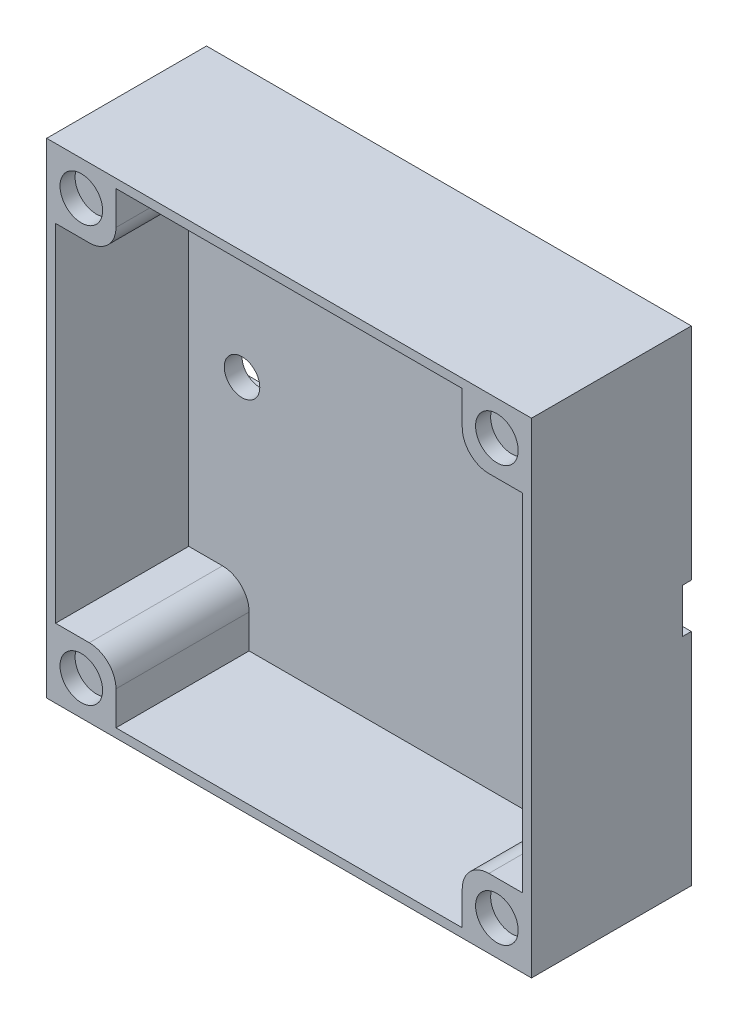
SolidWorks part; units mm, degrees
ref_plane "Přední rovina" through (0, 0, 0) normal (0, 0, 1) x (1, 0, 0)
ref_plane "Horní rovina" through (0, 0, 0) normal (0, 1, 0) x (1, 0, 0)
ref_plane "Pravá rovina" through (0, 0, 0) normal (1, 0, 0) x (0, 0, -1)
sketch "Skica1" plane through (0, 0, 0) normal (0, 0, 1) x (1, 0, 0)
  line L1 (27.3, 27.3) -> (-27.3, 27.3)
  line L2 (27.3, 27.3) -> (27.3, -27.3)
  line L3 (27.3, -27.3) -> (-27.3, -27.3)
  line L4 (-27.3, 27.3) -> (-27.3, -27.3)
  line L5 (27.3, 27.3) -> (-27.3, -27.3) construction
  line L6 (27.3, -27.3) -> (-27.3, 27.3) construction
  point P0 (0, 0)
  point P5 (-27.5, 0)
  point P11 (4.5, 0)
  dimension "D1" = 54.6
  dimension "D2" = 54.6
extrude "Přidat vysunutím2" add sketch "Skica1" along normal blind 3 contours L2 L1 L4 L3
sketch "Skica5" plane through (0, 0, 0) normal (0, 0, -1) x (-1, 0, 0)
  line L10 (27.3, 27.3) -> (27.3, -27.3) construction
  line L11 (-27.3, 2.5) -> (27.3, 2.5)
  line L12 (-27.3, 2.5) -> (-27.3, -2.5)
  line L13 (-27.3, -2.5) -> (27.3, -2.5)
  line L14 (27.3, 2.5) -> (27.3, -2.5)
  line L15 (-27.3, 2.5) -> (27.3, -2.5) construction
  line L16 (-27.3, -2.5) -> (27.3, 2.5) construction
  point P0 (0, 0)
  dimension "D1" = 5
extrude "Odebrat vysunutím3" cut sketch "Skica5" against normal blind 1 contours L11 L14 L13 L12
sketch "Skica14" plane through (0, 0, 3) normal (0, 0, 1) x (1, 0, 0)
  line L1 (-27.3, 27.3) -> (27.3, 27.3)
  line L2 (-27.3, 27.3) -> (-27.3, -27.3)
  line L3 (-27.3, -27.3) -> (27.3, -27.3)
  line L4 (27.3, 27.3) -> (27.3, -27.3)
  line L5 (-26.3, 26.3) -> (26.3, 26.3)
  line L6 (-26.3, 26.3) -> (-26.3, -27.3)
  line L7 (-26.3, -27.3) -> (26.3, -27.3)
  line L8 (26.3, 26.3) -> (26.3, -27.3)
  line L9 (-26.3, -27.3) -> (26.3, -27.3)
  line L10 (-26.3, -27.3) -> (-26.3, -26.3)
  line L11 (-26.3, -26.3) -> (26.3, -26.3)
  line L12 (26.3, -27.3) -> (26.3, -26.3)
  line M13 (-27.3, -27.3) -> (27.3, -27.3)
  line M14 (27.3, -27.3) -> (27.3, 27.3)
  line M15 (27.3, 27.3) -> (-27.3, 27.3)
  line M16 (-27.3, 27.3) -> (-27.3, -27.3)
  dimension "D1" = 1
  dimension "D2" = 1
  dimension "D3" = 1
  dimension "D4" = 0
  dimension "D5" = 1
  dimension "D6" = 52.6
extrude "Přidat vysunutím9" add sketch "Skica14" along normal blind 15 contours L5 L8 L6 M13 M14 M15 M16 | L10 L9 L12 L11
sketch "Skica17" plane through (0, 0, 1) normal (0, 0, -1) x (-1, 0, 0)
  line L0 (-27.3, 2.5) -> (-27.3, -2.5) construction
  line L1 (-12.5, -2.5) -> (-12.5, 2.5) construction
  line L2 (27.3, 2.5) -> (27.3, -2.5) construction
  circle A0 centre (-20.3, 0) radius 2
  circle A1 centre (20.3, 0) radius 2
  dimension "D1" = 4
  dimension "D2" = 4
  dimension "D3" = 7
  dimension "D4" = 7.8
  dimension "D5" = 7
extrude "Odebrat vysunutím8" cut sketch "Skica17" against normal blind 4
sketch "Skica19" plane through (0, 0, 0) normal (0, 0, -1) x (-1, 0, 0)
  line L1 (-27.3, 27.3) -> (-19.5, 27.3)
  line L2 (-27.3, 27.3) -> (-27.3, 19.5)
  line L3 (-27.3, 19.5) -> (-19.5, 19.5)
  line L4 (-19.5, 27.3) -> (-19.5, 19.5)
  line L5 (27.3, 27.3) -> (19.5, 27.3)
  line L6 (27.3, 27.3) -> (27.3, 19.5)
  line L7 (27.3, 19.5) -> (19.5, 19.5)
  line L8 (19.5, 27.3) -> (19.5, 19.5)
  line L9 (-27.3, -27.3) -> (-19.5, -27.3)
  line L10 (-27.3, -27.3) -> (-27.3, -19.5)
  line L11 (-27.3, -19.5) -> (-19.5, -19.5)
  line L12 (-19.5, -27.3) -> (-19.5, -19.5)
  line L13 (27.3, -27.3) -> (19.5, -27.3)
  line L14 (27.3, -27.3) -> (27.3, -19.5)
  line L15 (27.3, -19.5) -> (19.5, -19.5)
  line L16 (19.5, -27.3) -> (19.5, -19.5)
  dimension "D1" = 7.8
  dimension "D2" = 7.8
  dimension "D3" = 7.8
  dimension "D4" = 7.8
extrude "Přidat vysunutím10" add sketch "Skica19" against normal blind 18
sketch "Skica20" plane through (0, 0, 18) normal (0, 0, 1) x (1, 0, 0)
  line L0 (-27.3, -27.3) -> (27.3, -27.3) construction
  line L1 (-19.5, -26.3) -> (-19.5, -19.5) construction
  line L2 (-27.3, 27.3) -> (-27.3, -27.3) construction
  line L3 (27.3, 27.3) -> (-27.3, 27.3) construction
  line L4 (27.3, -27.3) -> (27.3, 27.3) construction
  line L5 (-27.3, -27.3) -> (27.3, -27.3) construction
  circle A0 centre (-23.4, -23.4) radius 2.4
  circle A1 centre (-23.4, 23.4) radius 2.4
  circle A2 centre (23.4003, 23.4) radius 2.4
  circle A3 centre (23.4003, -23.4) radius 2.4
  dimension "D1" = 4.8
  dimension "D4" = 4.8
  dimension "D5" = 3.9
  dimension "D7" = 4.8
  dimension "D10" = 4.8
  dimension "D2" = 3.9
  dimension "D3" = 3.9
  dimension "D6" = 3.9
  dimension "D8" = 3.8997
  dimension "D9" = 3.9
  dimension "D11" = 3.9
  dimension "D12" = 3.8997
extrude "Odebrat vysunutím9" cut sketch "Skica20" against normal blind 1.7
fillet "Zaoblit1" radius 3 4 edges at (19.5, 19.5, 10.5) (19.5, -19.5, 10.5) (-19.5, -19.5, 10.5) (-19.5, 19.5, 10.5)
